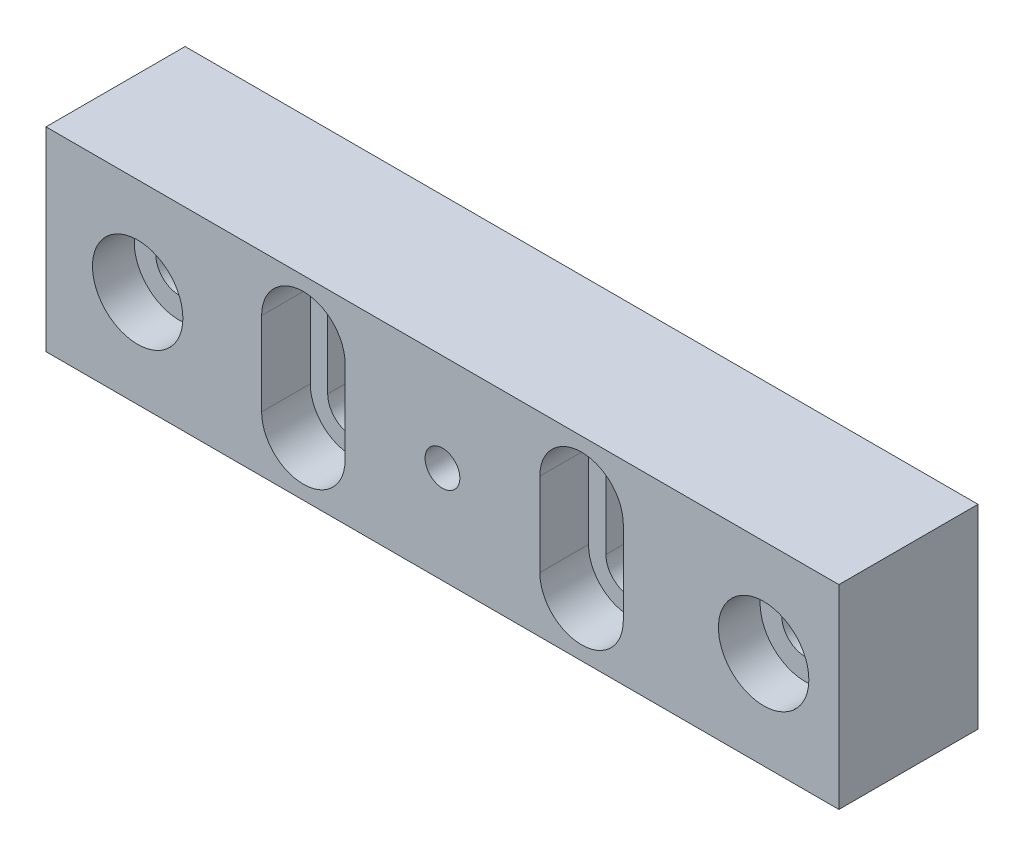
SolidWorks part; units mm, degrees
ref_plane "Front Plane" through (0, 0, 0) normal (0, 0, 1) x (1, 0, 0)
ref_plane "Top Plane" through (0, 0, 0) normal (0, 1, 0) x (1, 0, 0)
ref_plane "Right Plane" through (0, 0, 0) normal (1, 0, 0) x (0, 0, -1)
sketch "Sketch1" plane through (0, 0, 0) normal (0, 0, 1) x (1, 0, 0)
  line L5 (-28.5, -7) -> (28.5, -7)
  line L6 (-28.5, -7) -> (-28.5, 7)
  line L7 (-28.5, 7) -> (28.5, 7)
  line L8 (28.5, -7) -> (28.5, 7)
  line L9 (-28.5, -7) -> (28.5, 7) construction
  line L10 (-28.5, 7) -> (28.5, -7) construction
  point P0 (0, 0)
  dimension "D1" = 14
  dimension "D2" = 57
extrude "Boss-Extrude1" add sketch "Sketch1" along normal blind 10
sketch "Sketch2" plane through (0, 0, 10) normal (0, 0, 1) x (1, 0, 0)
  line L0 (-10, 3) -> (-10, -3) construction
  line L1 (-7, 3) -> (-7, -3)
  line L2 (-13, 3) -> (-13, -3)
  line L3 (10, 3) -> (10, -3) construction
  line L4 (13, 3) -> (13, -3)
  line L5 (7, 3) -> (7, -3)
  line L6 (-28.5, 7) -> (-28.5, -7) construction
  arc A0 (-7, 3) -> (-13, 3) centre (-10, 3) ccw
  arc A1 (-13, -3) -> (-7, -3) centre (-10, -3) ccw
  arc A2 (13, 3) -> (7, 3) centre (10, 3) ccw
  arc A3 (7, -3) -> (13, -3) centre (10, -3) ccw
  point P2 (-10, 0)
  point P7 (10, 0)
  point P14 (0, 0)
  point P15 (0, 0)
  dimension "D1" = 3
  dimension "D2" = 6
  dimension "D3" = 15.5
  dimension "D4" = 14
extrude "Cut-Extrude1" cut sketch "Sketch2" against normal blind 3.5
sketch "Sketch3" plane through (0, 0, 6.5) normal (0, 0, 1) x (1, 0, 0)
  line L6 (-11.75, 3) -> (-11.75, -3)
  line L7 (-8.25, -3) -> (-8.25, 3)
  line L8 (-11.75, 3) -> (-11.75, -3)
  line L9 (-8.25, -3) -> (-8.25, 3)
  line L19 (11.75, -3) -> (11.75, 3)
  line L20 (8.25, 3) -> (8.25, -3)
  line L21 (11.75, -3) -> (11.75, 3)
  line L22 (8.25, 3) -> (8.25, -3)
  arc A8 (-8.25, 3) -> (-11.75, 3) centre (-10, 3) ccw
  arc A9 (-11.75, -3) -> (-8.25, -3) centre (-10, -3) ccw
  arc A10 (-8.25, 3) -> (-11.75, 3) centre (-10, 3) ccw
  arc A11 (-11.75, -3) -> (-8.25, -3) centre (-10, -3) ccw
  arc A19 (8.25, -3) -> (11.75, -3) centre (10, -3) ccw
  arc A20 (11.75, 3) -> (8.25, 3) centre (10, 3) ccw
  arc A21 (8.25, -3) -> (11.75, -3) centre (10, -3) ccw
  arc A22 (11.75, 3) -> (8.25, 3) centre (10, 3) ccw
  dimension "D1" = 1.25
  dimension "D2" = 1.25
extrude "Cut-Extrude2" cut sketch "Sketch3" against normal through all
hole_wizard "CBORE for M3 SHCS1" positions "Sketch4" profile "Sketch5" counterbore size "M3" standard "ANSI Metric" end condition through all
sketch "Sketch4" plane through (0, 0, 10) normal (0, 0, 1) x (1, 0, 0)
  point P0 (-21.91, 0)
sketch "Sketch5" plane through (-21.91, 0, 10) normal (1, 0, 0) x (0, -1, 0)
  line L0 (0, 0) -> (0, 10)
  line L1 (0, 10) -> (1.7, 10)
  line L3 (1.7, 10) -> (1.7, 3)
  line L4 (1.7, 3) -> (3.25, 3)
  line L5 (3.25, 3) -> (3.25, 0)
  line L7 (3.25, 0) -> (0, 0)
  line L11 (0, -6.35) -> (0, 107.95) construction
  dimension "Thru Hole Dia." = 3.4
  dimension "Thru Hole Depth" = 10
  dimension "C'Bore Dia." = 6.5
  dimension "C'Bore Depth" = 3
pattern_linear "LPattern1" count 2 spacing 45 along (1, 0, 0) of "CBORE for M3 SHCS1"
hole_wizard "M3x0.5 Tapped Hole1" positions "Sketch6" profile "Sketch7" tap size "M3x0.5" standard "ANSI Metric" end condition through all
sketch "Sketch6" plane through (0, 0, 10) normal (0, 0, 1) x (1, 0, 0)
  point P0 (0, 0)
sketch "Sketch7" plane through (0, 0, 10) normal (1, 0, 0) x (0, -1, 0)
  line L0 (0, 0) -> (0, 10)
  line L1 (0, 10) -> (1.25, 10)
  line L2 (1.25, 10) -> (1.25, 0)
  line L5 (1.25, 0) -> (0, 0)
  line L11 (0, -6.35) -> (0, 107.95) construction
  dimension "Thru Tap Drill Dia." = 2.5
  dimension "Thru Tap Drill Depth" = 10
cosmetic thread "Hole Thread1" parameters "D2"=3
